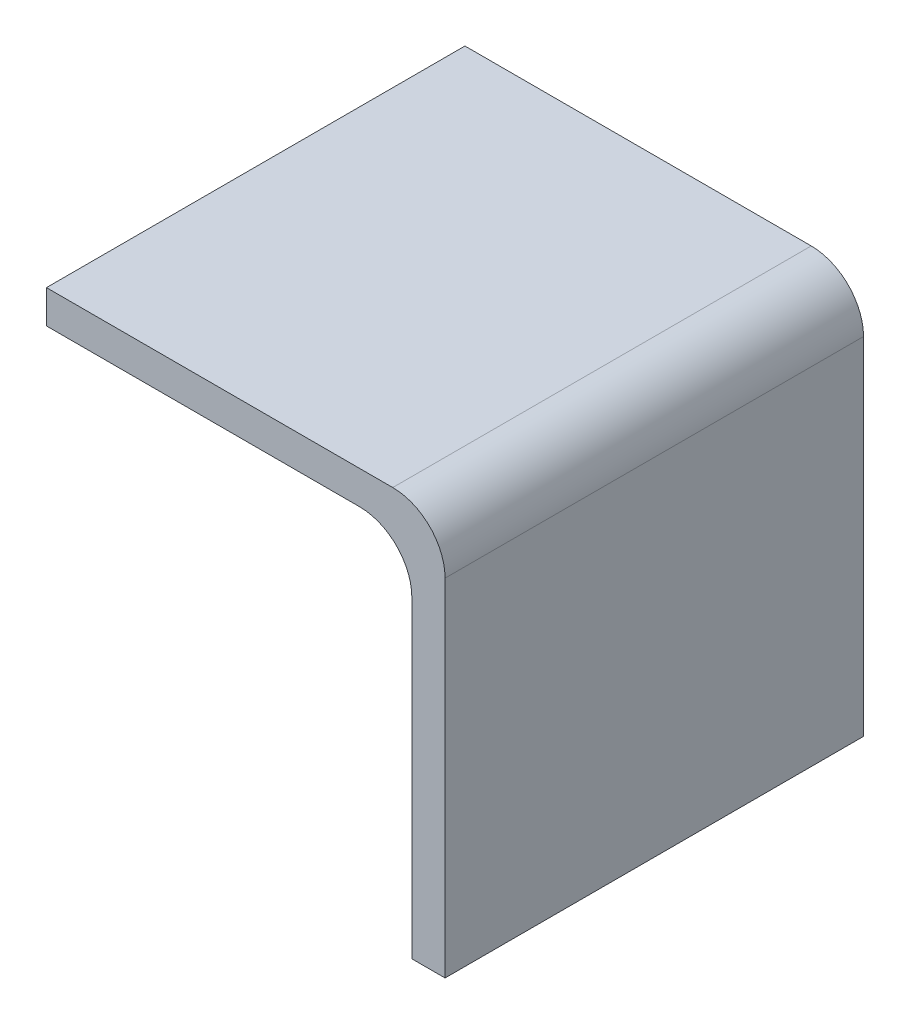
SolidWorks part; units mm, degrees
ref_plane "Front Plane" through (0, 0, 0) normal (0, 0, 1) x (1, 0, 0)
ref_plane "Top Plane" through (0, 0, 0) normal (0, 1, 0) x (1, 0, 0)
ref_plane "Right Plane" through (0, 0, 0) normal (1, 0, 0) x (0, 0, -1)
sketch "Sketch1" plane through (0, 0, 0) normal (0, 0, 1) x (1, 0, 0)
  line L0 (0, 0) -> (34.925, 0)
  line L1 (0, 0) -> (38.1, 0) construction
  line L2 (0, 0) -> (0, 3.175)
  line L3 (0, 3.175) -> (38.1, 3.175)
  line L4 (38.1, 0) -> (38.1, 3.175)
  line L5 (38.1, 0) -> (34.925, 0) construction
  line L6 (38.1, 0) -> (38.1, -34.925)
  line L7 (38.1, -34.925) -> (34.925, -34.925)
  line L8 (34.925, 0) -> (34.925, -34.925)
  dimension "D1" = 38.1
  dimension "D2" = 38.1
  dimension "D3" = 3.175
  dimension "D4" = 3.175
extrude "Boss-Extrude1" add sketch "Sketch1" along normal blind 40
fillet "Fillet1" radius 5 1 edges at (34.925, 0, 20)
fillet "Fillet2" radius 5 1 edges at (38.1, 3.175, 20)
ref_plane "Plane1" through (0, 0, 20) normal (0, 0, -1) x (-1, 0, 0)
